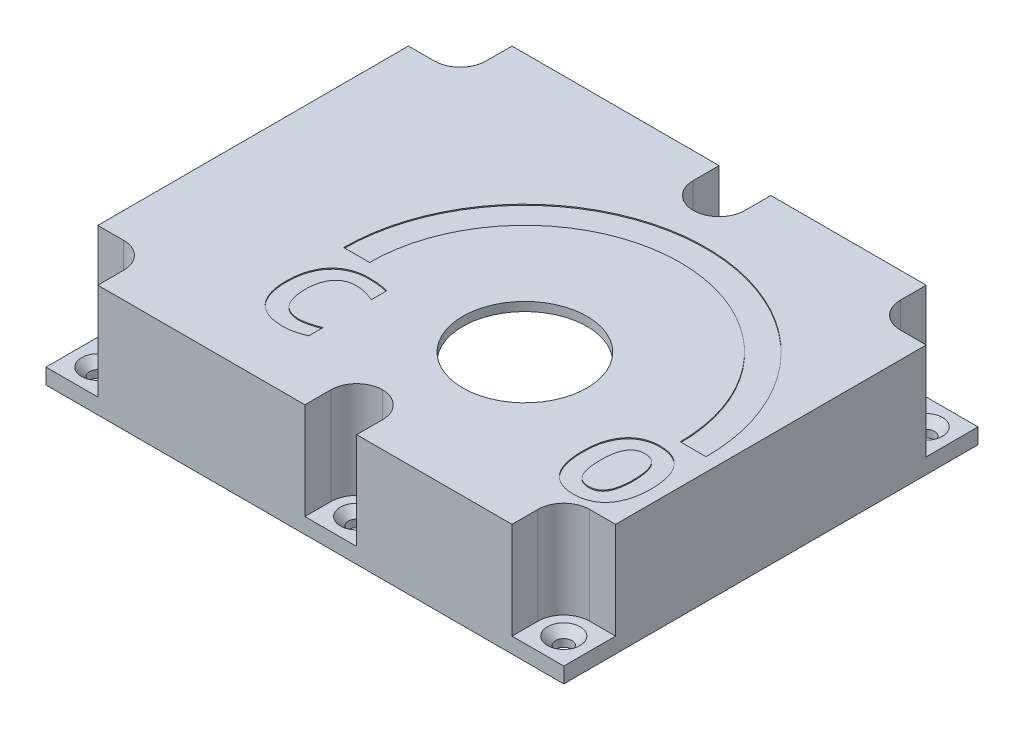
SolidWorks part; units mm, degrees
ref_plane "Płaszczyzna przednia" through (0, 0, 0) normal (0, 0, 1) x (1, 0, 0)
ref_plane "Płaszczyzna górna" through (0, 0, 0) normal (0, 1, 0) x (1, 0, 0)
ref_plane "Płaszczyzna prawa" through (0, 0, 0) normal (1, 0, 0) x (0, 0, -1)
sketch "Sketch1" plane through (0, 0, 0) normal (0, 1, 0) x (1, 0, 0)
  line L0 (-49.242, 28.8418) -> (-44.241, 28.8418)
  line L5 (-49.242, 38.8418) -> (0.758, 38.8418) construction
  line L18 (-49.242, 38.8418) -> (-49.242, -41.1582) construction
  line L19 (-49.242, -41.1582) -> (0.758, -41.1582) construction
  line L21 (50.758, 38.8418) -> (50.758, -41.1582) construction
  line L22 (-49.242, 38.8418) -> (-39.242, 38.8418) construction
  line L23 (-49.242, 38.8418) -> (-49.242, 28.8418) construction
  line L24 (-49.242, 28.8418) -> (-39.242, 28.8418) construction
  line L25 (-39.242, 38.8418) -> (-39.242, 28.8418) construction
  line L26 (50.758, 38.8418) -> (40.758, 38.8418) construction
  line L27 (50.758, 38.8418) -> (50.758, 28.8418) construction
  line L28 (50.758, 28.8418) -> (40.758, 28.8418) construction
  line L29 (40.758, 38.8418) -> (40.758, 28.8418) construction
  line L30 (50.758, -41.1582) -> (40.758, -41.1582) construction
  line L31 (50.758, -41.1582) -> (50.758, -31.1582) construction
  line L32 (50.758, -31.1582) -> (40.758, -31.1582) construction
  line L33 (40.758, -41.1582) -> (40.758, -31.1582) construction
  line L34 (-49.242, -41.1582) -> (-39.242, -41.1582) construction
  line L35 (-49.242, -41.1582) -> (-49.242, -31.1582) construction
  line L36 (-49.242, -31.1582) -> (-39.242, -31.1582) construction
  line L37 (-39.242, -41.1582) -> (-39.242, -31.1582) construction
  line L39 (0.758, 28.8418) -> (10.758, 28.8418) construction
  line L40 (0.758, 28.8418) -> (10.758, 28.8418) construction
  line L41 (0.758, 28.8418) -> (0.758, 38.8418) construction
  line L43 (10.758, 28.8418) -> (10.758, 38.8418) construction
  line L48 (0.758, -41.1582) -> (0.758, -31.1582) construction
  line L49 (0.758, -31.1582) -> (10.758, -31.1582) construction
  line L50 (10.758, -41.1582) -> (10.758, -31.1582) construction
  line L51 (-39.242, 33.8408) -> (-39.242, 38.8418)
  line L52 (0.758, 38.8418) -> (0.758, 33.8408)
  line L53 (5.757, 28.8418) -> (5.759, 28.8418)
  line L54 (10.758, 33.8408) -> (10.758, 38.8418)
  line L55 (40.758, 38.8418) -> (40.758, 33.8408)
  line L56 (45.757, 28.8418) -> (50.758, 28.8418)
  line L57 (50.758, -31.1582) -> (45.757, -31.1582)
  line L58 (40.758, -36.1572) -> (40.758, -41.1582)
  line L59 (10.758, -41.1582) -> (10.758, -36.1572)
  line L60 (5.759, -31.1582) -> (5.757, -31.1582)
  line L61 (0.758, -36.1572) -> (0.758, -41.1582)
  line L62 (-39.242, -41.1582) -> (-39.242, -36.1572)
  line L63 (-44.241, -31.1582) -> (-49.242, -31.1582)
  line L64 (-47.742, 27.3418) -> (-44.241, 27.3418)
  line L65 (-49.242, 38.8418) -> (-37.742, 38.8418) construction
  line L66 (-49.242, 38.8418) -> (-49.242, 27.3418) construction
  line L69 (-37.742, 33.8408) -> (-37.742, 37.3418)
  line L70 (-37.742, -39.6582) -> (-37.742, -36.1572)
  line L71 (-44.241, -29.6582) -> (-47.742, -29.6582)
  line L72 (39.258, 37.3418) -> (39.258, 33.8408)
  line L73 (45.757, 27.3418) -> (49.258, 27.3418)
  line L74 (39.258, -39.6582) -> (39.258, -36.1572)
  line L75 (45.757, -29.6582) -> (49.258, -29.6582)
  line L76 (-0.742, 37.3418) -> (-0.742, 33.8408)
  line L77 (5.757, 27.3418) -> (5.759, 27.3418)
  line L78 (12.258, 33.8408) -> (12.258, 37.3418)
  line L79 (-0.742, -39.6582) -> (-0.742, -36.1572)
  line L80 (5.757, -29.6582) -> (5.759, -29.6582)
  line L81 (12.258, -36.1572) -> (12.258, -39.6582)
  line L82 (-37.742, -39.6582) -> (-0.742, -39.6582)
  line L83 (-47.742, -29.6582) -> (-47.742, 27.3418)
  line L84 (-37.742, 37.3418) -> (-0.742, 37.3418)
  line L85 (49.258, -29.6582) -> (49.258, 27.3418)
  line L86 (10.758, -41.1582) -> (50.758, -41.1582) construction
  line L87 (12.258, 37.3418) -> (39.258, 37.3418)
  line L88 (-49.242, -31.1582) -> (-49.242, 28.8418)
  line L89 (12.258, -39.6582) -> (39.258, -39.6582)
  line L90 (10.758, 38.8418) -> (50.758, 38.8418) construction
  line L91 (-39.242, 38.8418) -> (0.758, 38.8418)
  line L92 (10.758, 38.8418) -> (40.758, 38.8418)
  line L93 (50.758, 28.8418) -> (50.758, -31.1582)
  line L94 (40.758, -41.1582) -> (10.758, -41.1582)
  line L95 (0.758, -41.1582) -> (-39.242, -41.1582)
  arc A0 (-39.242, -36.1572) -> (-44.241, -31.1582) centre (-44.241, -36.1572) ccw
  arc A1 (5.757, -31.1582) -> (0.758, -36.1572) centre (5.757, -36.1572) ccw
  arc A2 (10.758, -36.1572) -> (5.759, -31.1582) centre (5.759, -36.1572) ccw
  arc A3 (45.757, -31.1582) -> (40.758, -36.1572) centre (45.757, -36.1572) ccw
  arc A4 (40.758, 33.8408) -> (45.757, 28.8418) centre (45.757, 33.8408) ccw
  arc A5 (5.759, 28.8418) -> (10.758, 33.8408) centre (5.759, 33.8408) ccw
  arc A6 (0.758, 33.8408) -> (5.757, 28.8418) centre (5.757, 33.8408) ccw
  arc A7 (-44.241, 28.8418) -> (-39.242, 33.8408) centre (-44.241, 33.8408) ccw
  arc A8 (-37.742, -36.1572) -> (-44.241, -29.6582) centre (-44.241, -36.1572) ccw
  arc A9 (-0.742, -36.1572) -> (5.757, -29.6582) centre (5.757, -36.1572) cw
  arc A10 (5.759, -29.6582) -> (12.258, -36.1572) centre (5.759, -36.1572) cw
  arc A11 (39.258, -36.1572) -> (45.757, -29.6582) centre (45.757, -36.1572) cw
  arc A12 (39.258, 33.8408) -> (45.757, 27.3418) centre (45.757, 33.8408) ccw
  arc A13 (5.759, 27.3418) -> (12.258, 33.8408) centre (5.759, 33.8408) ccw
  arc A14 (-0.742, 33.8408) -> (5.757, 27.3418) centre (5.757, 33.8408) ccw
  arc A15 (-44.241, 27.3418) -> (-37.742, 33.8408) centre (-44.241, 33.8408) ccw
  point P53 (50.758, 27.3418)
  point P55 (39.258, 38.8418)
  point P61 (-0.742, 38.8418)
  point P81 (39.258, 27.3418)
  point P86 (-0.742, 27.3418)
  point P89 (-37.742, 27.3418)
  point P90 (-37.742, -39.6582)
  point P93 (-47.742, -29.6582)
  point P96 (-37.742, 37.3418)
  point P99 (49.258, -29.6582)
  dimension "D3" = 4.999
  dimension "D9" = 6.499
  dimension "D1" = 100
  dimension "D2" = 80
  dimension "D4" = 11.5
  dimension "D5" = 11.5
  dimension "D6" = 11.5
  dimension "D7" = 11.5
  dimension "D8" = 1.5
  dimension "D12" = 1.5
extrude "Boss-Extrude4" add sketch "Sketch1" along normal blind 20
sketch "Sketch2" plane through (0, 0, 0) normal (0, -1, 0) x (1, 0, 0)
  line L0 (0.758, 41.1582) -> (10.758, 41.1582) construction
  line L1 (-49.242, 31.1582) -> (-39.242, 31.1582) construction
  line L2 (-49.242, 31.1582) -> (-49.242, 41.1582) construction
  line L3 (-49.242, 41.1582) -> (-39.242, 41.1582) construction
  line L4 (-39.242, 31.1582) -> (-39.242, 41.1582) construction
  line L5 (40.758, 41.1582) -> (50.758, 41.1582) construction
  line L6 (40.758, 41.1582) -> (40.758, 31.1582) construction
  line L7 (40.758, 31.1582) -> (50.758, 31.1582) construction
  line L8 (50.758, 41.1582) -> (50.758, 31.1582) construction
  line L9 (-49.242, -28.8418) -> (-39.242, -28.8418) construction
  line L10 (-49.242, -28.8418) -> (-49.242, -38.8418) construction
  line L11 (-49.242, -38.8418) -> (-39.242, -38.8418) construction
  line L12 (-39.242, -28.8418) -> (-39.242, -38.8418) construction
  line L13 (50.758, -28.8418) -> (40.758, -28.8418) construction
  line L14 (50.758, -28.8418) -> (50.758, -38.8418) construction
  line L15 (50.758, -38.8418) -> (40.758, -38.8418) construction
  line L16 (40.758, -28.8418) -> (40.758, -38.8418) construction
  line L17 (0.758, 41.1582) -> (0.758, 31.1582) construction
  line L18 (10.758, 41.1582) -> (10.758, 31.1582) construction
  line L19 (0.758, 31.1582) -> (10.758, 31.1582) construction
  line L20 (0.758, -38.8418) -> (10.758, -38.8418) construction
  line L21 (0.758, -38.8418) -> (0.758, -28.8418) construction
  line L22 (10.758, -38.8418) -> (10.758, -28.8418) construction
  line L23 (0.758, -28.8418) -> (10.758, -28.8418) construction
  line L24 (0.758, -38.8418) -> (10.758, -38.8418)
  line L25 (-49.242, -38.8418) -> (-39.242, -38.8418)
  line L26 (-49.242, -38.8418) -> (-49.242, -28.8418)
  line L27 (-49.242, -28.8418) -> (-44.241, -28.8418)
  line L28 (-39.242, -38.8418) -> (-39.242, -33.8408)
  line L29 (-49.242, 41.1582) -> (-39.242, 41.1582)
  line L30 (-49.242, 41.1582) -> (-49.242, 31.1582)
  line L31 (-49.242, 31.1582) -> (-44.241, 31.1582)
  line L32 (-39.242, 41.1582) -> (-39.242, 36.1572)
  line L33 (50.758, 41.1582) -> (40.758, 41.1582)
  line L34 (50.758, 41.1582) -> (50.758, 31.1582)
  line L35 (50.758, 31.1582) -> (45.757, 31.1582)
  line L36 (40.758, 41.1582) -> (40.758, 36.1572)
  line L37 (50.758, -38.8418) -> (40.758, -38.8418)
  line L38 (50.758, -38.8418) -> (50.758, -28.8418)
  line L39 (50.758, -28.8418) -> (45.757, -28.8418)
  line L40 (40.758, -38.8418) -> (40.758, -33.8408)
  line L41 (10.758, -38.8418) -> (10.758, -33.8408)
  line L42 (5.759, -28.8418) -> (5.757, -28.8418)
  line L43 (0.758, -33.8408) -> (0.758, -38.8418)
  line L44 (0.758, 41.1582) -> (10.758, 41.1582)
  line L45 (10.758, 41.1582) -> (10.758, 36.1572)
  line L46 (5.759, 31.1582) -> (5.757, 31.1582)
  line L47 (0.758, 36.1572) -> (0.758, 41.1582)
  arc A0 (-44.241, -28.8418) -> (-39.242, -33.8408) centre (-44.241, -33.8408) cw
  arc A1 (45.757, 31.1582) -> (40.758, 36.1572) centre (45.757, 36.1572) cw
  arc A2 (45.757, -28.8418) -> (40.758, -33.8408) centre (45.757, -33.8408) ccw
  arc A3 (5.757, -28.8418) -> (0.758, -33.8408) centre (5.757, -33.8408) ccw
  arc A4 (10.758, -33.8408) -> (5.759, -28.8418) centre (5.759, -33.8408) ccw
  arc A5 (10.758, 36.1572) -> (5.759, 31.1582) centre (5.759, 36.1572) cw
  arc A6 (5.757, 31.1582) -> (0.758, 36.1572) centre (5.757, 36.1572) cw
  arc A7 (-44.241, 31.1582) -> (-39.242, 36.1572) centre (-44.241, 36.1572) ccw
  dimension "D1" = 4.999
extrude "Boss-Extrude5" add sketch "Sketch2" against normal blind 3
sketch "Sketch3" plane through (0, 20, 0) normal (0, 1, 0) x (1, 0, 0)
  line L0 (0.758, -41.1582) -> (0.758, -36.1572)
  line L1 (-49.242, 38.8418) -> (50.758, 38.8418) construction
  line L2 (-49.242, 38.8418) -> (-49.242, -41.1582) construction
  line L3 (-49.242, -41.1582) -> (50.758, -41.1582) construction
  line L4 (50.758, 38.8418) -> (50.758, -41.1582) construction
  line L5 (-49.242, 38.8418) -> (-39.242, 38.8418)
  line L6 (-49.242, 38.8418) -> (-49.242, 28.8418)
  line L7 (-49.242, 28.8418) -> (-44.241, 28.8418)
  line L8 (-39.242, 38.8418) -> (-39.242, 33.8408)
  line L9 (50.758, 38.8418) -> (40.758, 38.8418)
  line L10 (50.758, 38.8418) -> (50.758, 28.8418)
  line L11 (50.758, 28.8418) -> (45.757, 28.8418)
  line L12 (40.758, 38.8418) -> (40.758, 33.8408)
  line L13 (50.758, -41.1582) -> (40.758, -41.1582)
  line L14 (50.758, -41.1582) -> (50.758, -31.1582)
  line L15 (50.758, -31.1582) -> (45.757, -31.1582)
  line L16 (40.758, -41.1582) -> (40.758, -36.1572)
  line L17 (-49.242, -41.1582) -> (-39.242, -41.1582)
  line L18 (-49.242, -41.1582) -> (-49.242, -31.1582)
  line L19 (-49.242, -31.1582) -> (-44.241, -31.1582)
  line L20 (-39.242, -41.1582) -> (-39.242, -36.1572)
  line L21 (10.758, -41.1582) -> (10.758, -36.1572)
  line L22 (5.759, -31.1582) -> (5.757, -31.1582)
  line L23 (0.758, 38.8418) -> (0.758, 33.8408)
  line L24 (5.757, 28.8418) -> (5.759, 28.8418)
  line L25 (10.758, 33.8408) -> (10.758, 38.8418)
  line L26 (-49.242, -31.1582) -> (-49.242, 28.8418)
  line L27 (-39.242, 38.8418) -> (0.758, 38.8418)
  line L28 (10.758, 38.8418) -> (40.758, 38.8418)
  line L29 (50.758, 28.8418) -> (50.758, -31.1582)
  line L30 (40.758, -41.1582) -> (10.758, -41.1582)
  line L31 (0.758, -41.1582) -> (-39.242, -41.1582)
  arc A0 (45.757, 28.8418) -> (40.758, 33.8408) centre (45.757, 33.8408) cw
  arc A1 (-44.241, 28.8418) -> (-39.242, 33.8408) centre (-44.241, 33.8408) ccw
  arc A2 (-44.241, -31.1582) -> (-39.242, -36.1572) centre (-44.241, -36.1572) cw
  arc A3 (45.757, -31.1582) -> (40.758, -36.1572) centre (45.757, -36.1572) ccw
  arc A4 (10.758, -36.1572) -> (5.759, -31.1582) centre (5.759, -36.1572) ccw
  arc A5 (0.758, -36.1572) -> (5.757, -31.1582) centre (5.757, -36.1572) cw
  arc A6 (5.759, 28.8418) -> (10.758, 33.8408) centre (5.759, 33.8408) ccw
  arc A7 (0.758, 33.8408) -> (5.757, 28.8418) centre (5.757, 33.8408) ccw
  dimension "D1" = 4.999
extrude "Boss-Extrude6" add sketch "Sketch3" along normal blind 1.7 contours A7 L23 L27 L8 A1 L7 L26 L19 A2 L20 L31 L0 A5 L22 A4 L21 L30 L16 A3 L15 L29 L11 A0 L12 L28 L25 A6 L24
sketch "Sketch6" plane through (0, 3, 0) normal (0, 1, 0) x (1, 0, 0)
  point P0 (-44.241, 33.8408)
  point P3 (45.757, 33.8408)
  point P6 (45.757, -36.1572)
  point P9 (-44.241, -36.1572)
  point P12 (5.757, -36.1572)
  point P15 (5.757, 33.8408)
hole_wizard "CSK for M3 Countersunk Flat Head Screw1" positions "Sketch6" profile "Sketch5" countersink size "M3" standard "ISO" end condition through all
sketch "Sketch5" plane through (-44.241, 3, -33.8408) normal (1, 0, 0) x (0, 0, 1)
  line L0 (0, 0) -> (0, 3)
  line L1 (0, 3) -> (1.6, 3)
  line L2 (1.6, 3) -> (1.6, 1.55)
  line L3 (1.6, 1.55) -> (3.15, 0)
  line L5 (3.15, 0) -> (0, 0)
  line L6 (-1.6, 1.55) -> (-3.15, 0) construction
  line L11 (0, -6.35) -> (0, 107.95) construction
  dimension "Thru Hole Dia." = 3.2
  dimension "Thru Hole Depth" = 3
  dimension "Near C'Sink Dia." = 6.3
  dimension "Near C'Sink Angle" = 90
sketch "Sketch7" plane through (0, 21.7, 0) normal (0, 1, 0) x (1, 0, 0)
  line L0 (50.758, 28.8418) -> (50.758, -31.1582) construction
  line L1 (40.758, -41.1582) -> (10.758, -41.1582) construction
  circle A0 centre (13.1964, -11.1082) radius 12
  point P0 (13.1964, -11.1082)
  dimension "D1" = 37.5616
  dimension "D2" = 30.05
extrude "Cut-Extrude1" cut sketch "Sketch7" against normal through all
sketch "Sketch8" plane through (0, 21.7, 0) normal (0, 1, 0) x (1, 0, 0)
  line L0 (-21.8036, -11.1082) -> (-16.8036, -11.1082)
  line L1 (13.1964, -11.1082) -> (-16.8036, -11.1082) construction
  line L4 (43.1964, -11.1082) -> (48.1964, -11.1082)
  arc A1 (-21.8036, -11.1082) -> (48.1964, -11.1082) centre (13.1964, -11.1082) cw
  arc A2 (-16.8036, -11.1082) -> (43.1964, -11.1082) centre (13.1964, -11.1082) cw
  text T0 "<b>C</b>" font "Consolas" height 16
  text T1 "O" font "Consolas" height 16
  point P5 (-21.8036, -11.1082)
  dimension "D1" = 30
  dimension "D3" = 35
extrude "Cut-Extrude2" cut sketch "Sketch8" against normal blind 0.2
